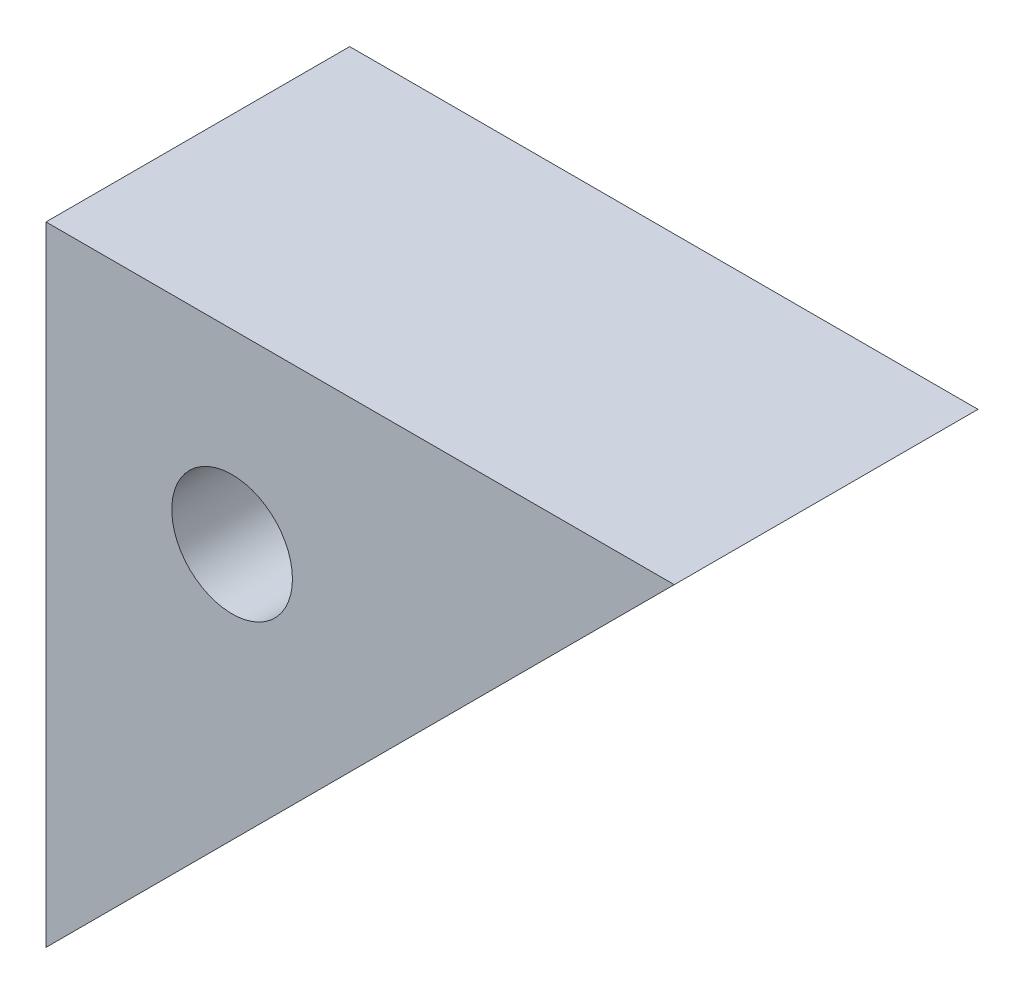
SolidWorks part; units mm, degrees
ref_plane "Front Plane" through (0, 0, 0) normal (0, 0, 1) x (1, 0, 0)
ref_plane "Top Plane" through (0, 0, 0) normal (0, 1, 0) x (1, 0, 0)
ref_plane "Right Plane" through (0, 0, 0) normal (1, 0, 0) x (0, 0, -1)
sketch "Sketch1" plane through (0, 0, 0) normal (0, 0, 1) x (1, 0, 0)
  line L0 (-33.2, 56.7) -> (-33.2, 44.7)
  line L1 (-33.2, -62.5) -> (-33.2, 62.5) construction
  line L2 (-33.2, 44.7) -> (-21.2, 56.7)
  line L3 (-33.2, 56.7) -> (33.2, 56.7) construction
  line L4 (-21.2, 56.7) -> (-33.2, 56.7)
  dimension "D1" = 12
extrude "Boss-Extrude1" add sketch "Sketch1" against normal blind 5.8 contours L2 L4 L0
hole_wizard "#6-32 Tapped Hole4" positions "Sketch3" profile "Sketch2" tap size "#6-32" standard "ANSI Inch" end condition up to next
sketch "Sketch3" plane through (0, 0, 0) normal (0, 0, 1) x (1, 0, 0)
  line L0 (-33.2, 56.7) -> (-27.2, 50.7) construction
  line L1 (-33.2, 44.7) -> (-21.2, 56.7) construction
  point P0 (-28.6754, 25)
  point P1 (-29.6458, 53.1458)
sketch "Sketch2" plane through (-28.6754, 25, 0) normal (1, 0, 0) x (0, -1, 0)
  line L0 (0, 0) -> (0, 5.8)
  line L1 (0, 5.8) -> (1.1526, 5.8)
  line L2 (1.1526, 5.8) -> (1.1526, 0)
  line L5 (1.1526, 0) -> (0, 0)
  line L11 (0, -6.35) -> (0, 107.95) construction
  dimension "Thread Major Dia." = 2.3051
  dimension "Thru Tap Drill Depth" = 5.8
